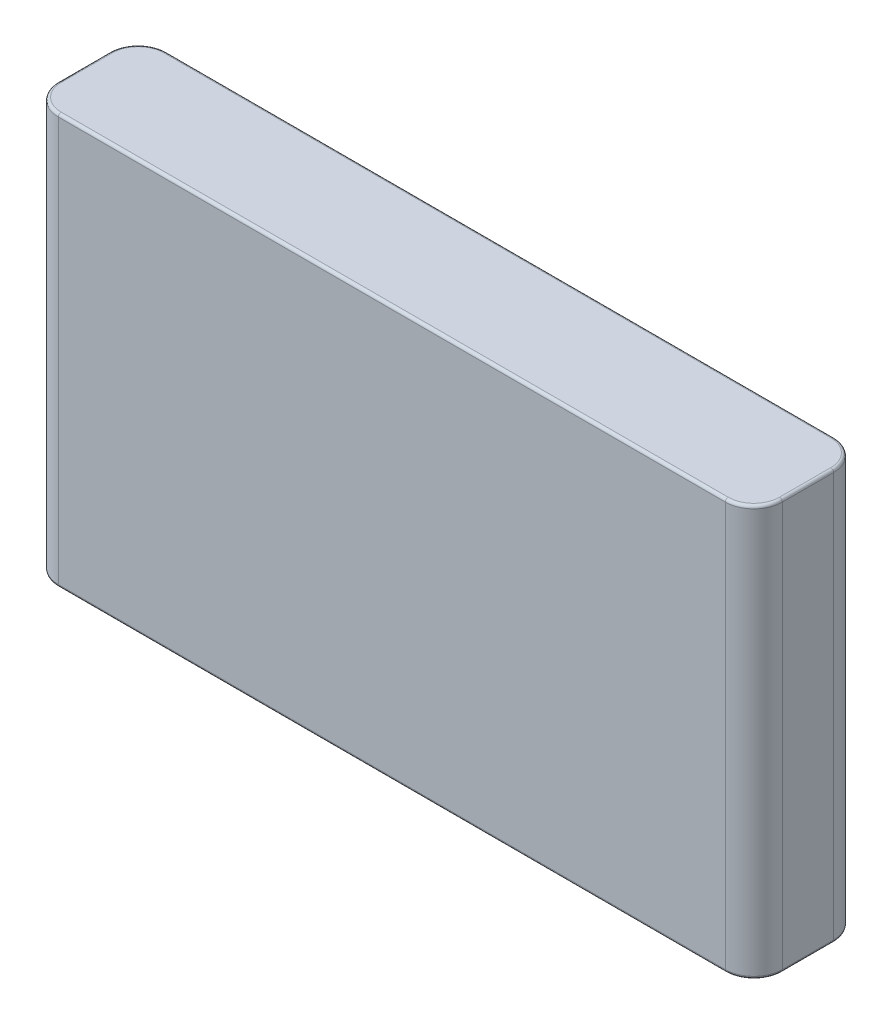
SolidWorks part; units mm, degrees
ref_plane "Plan de face" through (0, 0, 0) normal (0, 0, 1) x (1, 0, 0)
ref_plane "Plan de dessus" through (0, 0, 0) normal (0, 1, 0) x (1, 0, 0)
ref_plane "Plan de droite" through (0, 0, 0) normal (1, 0, 0) x (0, 0, -1)
sketch "Esquisse1" plane through (0, 0, 0) normal (0, 0, 1) x (1, 0, 0)
  line L1 (-63.5, -36) -> (63.5, -36)
  line L2 (-63.5, -36) -> (-63.5, 36)
  line L3 (-63.5, 36) -> (63.5, 36)
  line L4 (63.5, -36) -> (63.5, 36)
  line L5 (-63.5, -36) -> (63.5, 36) construction
  line L6 (-63.5, 36) -> (63.5, -36) construction
  point P0 (0, 0)
  dimension "D1" = 72
  dimension "D2" = 127
extrude "Boss.-Extru.1" add sketch "Esquisse1" along normal blind 19
fillet "Congé1" radius 5 4 edges at (63.5, 0, 0) (63.5, 0, 19) (-63.5, 0, 0) (-63.5, 0, 19)
fillet "Congé2" radius 0.5 16 edges at (62.0355, 36, 17.5355) (63.5, 36, 9.5) (62.0355, 36, 1.4645) (0, 36, 0) (-62.0355, 36, 1.4645) (-63.5, 36, 9.5) (-62.0355, 36, 17.5355) (-62.0355, -36, 17.5355) (-63.5, -36, 9.5) (-62.0355, -36, 1.4645) (0, -36, 0) (62.0355, -36, 1.4645) (63.5, -36, 9.5) (62.0355, -36, 17.5355) (0, 36, 19) (0, -36, 19)
